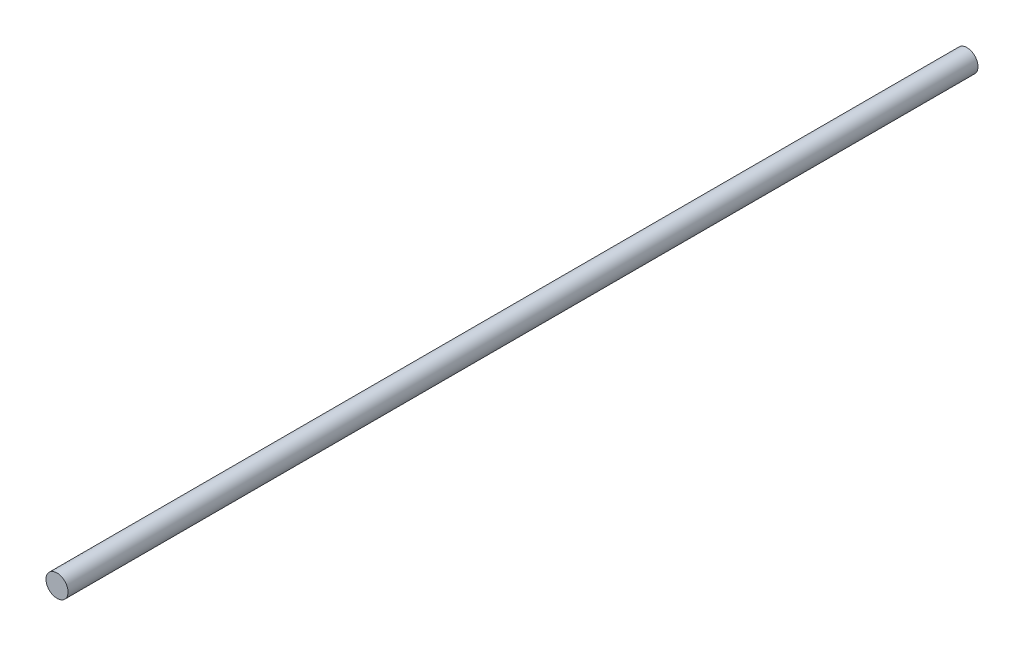
SolidWorks part; units mm, degrees
ref_plane "Front Plane" through (0, 0, 0) normal (0, 0, 1) x (1, 0, 0)
ref_plane "Top Plane" through (0, 0, 0) normal (0, 1, 0) x (1, 0, 0)
ref_plane "Right Plane" through (0, 0, 0) normal (1, 0, 0) x (0, 0, -1)
sketch "Sketch1" plane through (0, 0, 0) normal (0, 0, 1) x (1, 0, 0)
  circle A0 centre (0, 0) radius 4
extrude "Boss-Extrude1" add sketch "Sketch1" along normal blind 330
